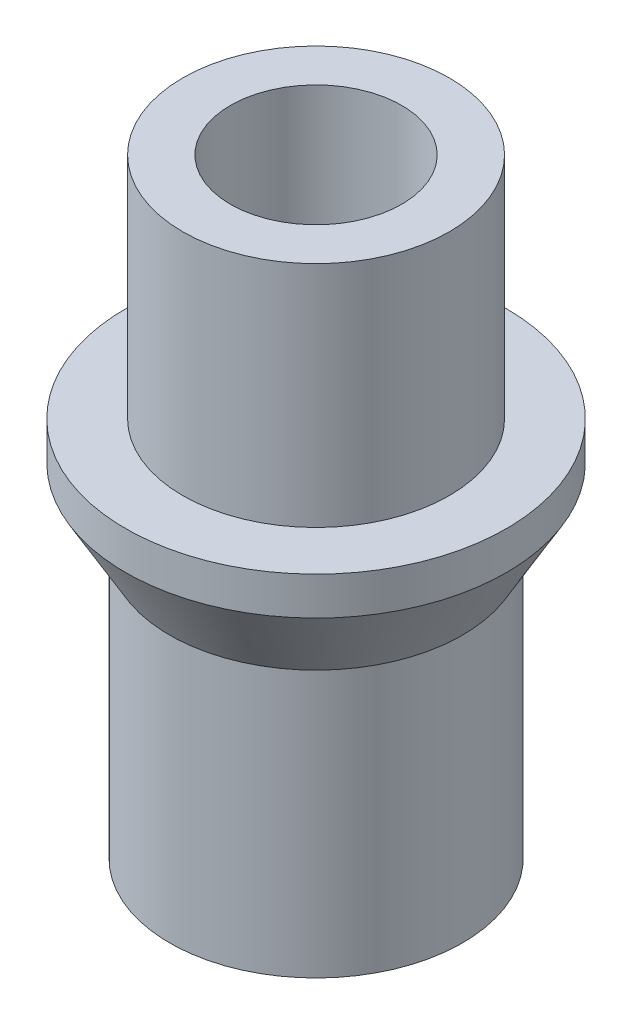
SolidWorks part; units mm, degrees
ref_plane "Front Plane" through (0, 0, 0) normal (0, 0, 1) x (1, 0, 0)
ref_plane "Top Plane" through (0, 0, 0) normal (0, 1, 0) x (1, 0, 0)
ref_plane "Right Plane" through (0, 0, 0) normal (1, 0, 0) x (0, 0, -1)
sketch "Sketch1" plane through (0, 0, 0) normal (0, 1, 0) x (1, 0, 0)
  circle A0 centre (0, 0) radius 3.5
  circle A1 centre (0, 0) radius 2.25
  dimension "D1" = 7
  dimension "D2" = 4.5
extrude "Boss-Extrude1" add sketch "Sketch1" against normal blind 6
sketch "Sketch2" plane through (0, -6, 0) normal (0, -1, 0) x (1, 0, 0)
  circle A0 centre (0, 0) radius 5
  dimension "D1" = 10
extrude "Boss-Extrude2" add sketch "Sketch2" along normal blind 1
sketch "Sketch4" plane through (0, -7, 0) normal (0, -1, 0) x (1, 0, 0)
  circle A0 centre (0, 0) radius 5
  dimension "D1" = 10
extrude "Boss-Extrude4" add sketch "Sketch4" along normal blind 2 draft 30
sketch "Sketch5" plane through (0, -9, 0) normal (0, -1, 0) x (1, 0, 0)
  circle A0 centre (0, 0) radius 3.8453
  dimension "D1" = 7.6906
extrude "Boss-Extrude5" add sketch "Sketch5" along normal blind 7
